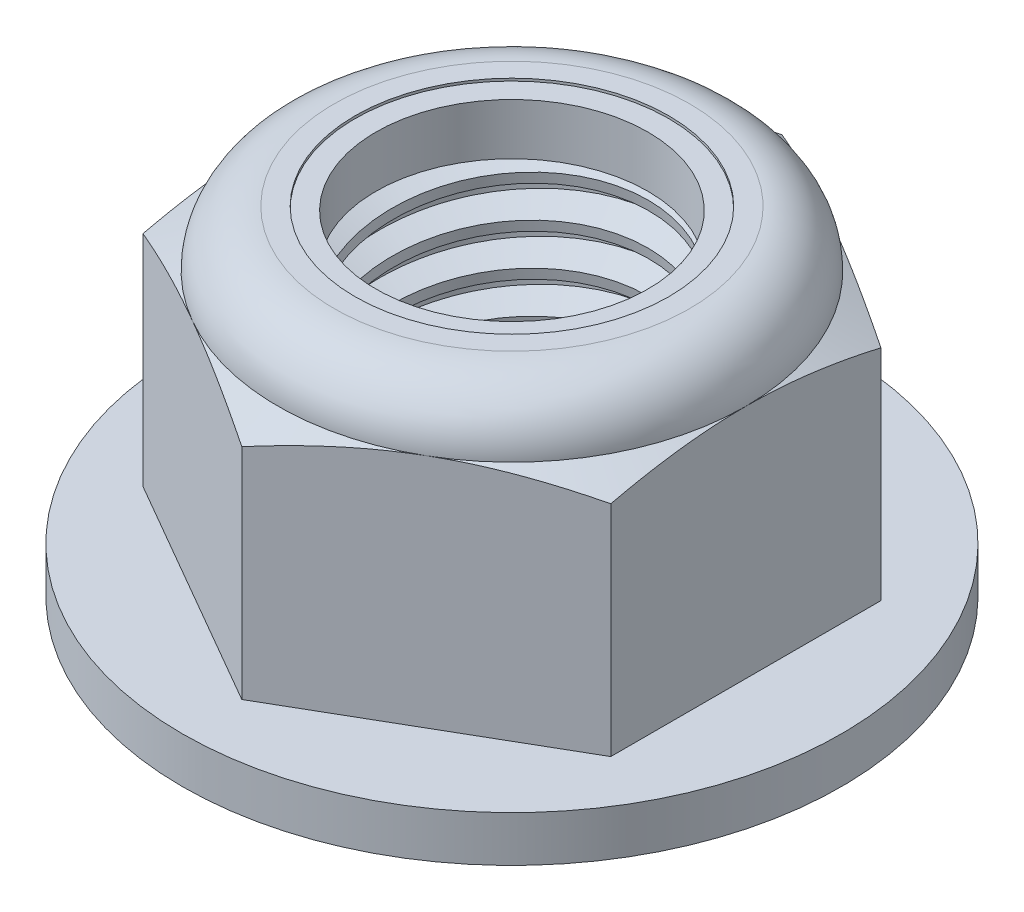
SolidWorks part; units mm, degrees
ref_plane "Front" through (0, 0, 0) normal (0, 0, 1) x (1, 0, 0)
ref_plane "Top" through (0, 0, 0) normal (0, 1, 0) x (1, 0, 0)
ref_plane "Right" through (0, 0, 0) normal (1, 0, 0) x (0, 0, -1)
sketch "Sketch1" plane through (0, 0, 0) normal (0, 1, 0) x (1, 0, 0)
  line L1 (0, 16.4978) -> (-14.2875, 8.2489)
  line L2 (-14.2875, 8.2489) -> (-14.2875, -8.2489)
  line L3 (-14.2875, -8.2489) -> (0, -16.4978)
  line L4 (0, -16.4978) -> (14.2875, -8.2489)
  line L5 (14.2875, -8.2489) -> (14.2875, 8.2489)
  line L6 (14.2875, 8.2489) -> (0, 16.4978)
  circle A0 centre (0, 0) radius 14.2875 construction
  dimension "Hex Flats" = 28.575
extrude "Extrude1" add sketch "Sketch1" along normal blind 20.6375
sketch "Sketch8" plane through (0, 0, 0) normal (1, 0, 0) x (0, 0, -1)
  line L0 (0, 0) -> (20.1295, 0)
  line L1 (20.1295, 0) -> (20.1295, 2.794)
  line L2 (20.1295, 2.794) -> (0, 2.794)
  line L3 (0, 2.794) -> (0, 0)
  line L4 (0, 0) -> (0, -2.794) construction
  dimension "Flange Height" = 2.794
  dimension "Flange Dia" = 40.259
revolve "Revolve3" add sketch "Sketch8" angle 360 about L4
sketch "Sketch2" plane through (0, 0, 0) normal (1, 0, 0) x (0, 0, -1)
  line L0 (-9.525, 0) -> (-9.525, 20.6375) construction
  line L1 (0, 0) -> (9.525, 0)
  line L2 (0, 0) -> (0, 20.6375)
  line L3 (0, 20.6375) -> (9.525, 20.6375)
  line L4 (9.525, 0) -> (9.525, 20.6375)
  line L5 (-8.2489, 20.6375) -> (8.2489, 20.6375) construction
  line L7 (0, -9.525) -> (0, 0) construction
  dimension "Thread Dia" = 19.05
revolve "Revolve1" add sketch "Sketch2" angle 360 about L7
sketch "Sketch3" plane through (0, 0, 0) normal (1, 0, 0) x (0, 0, -1)
  line L0 (9.525, 20.6375) -> (-9.525, 20.6375) construction
  line L1 (-9.525, 20.6375) -> (-9.525, 18.0975) construction
  line L2 (-9.525, 18.0975) -> (9.525, 20.6375) construction
  line L3 (9.525, 20.6375) -> (9.567, 20.3228) construction
  line L4 (9.567, 20.3228) -> (9.8607, 18.1198)
  line L5 (9.8607, 18.1198) -> (8.393, 18.7249)
  line L6 (8.393, 18.7249) -> (8.3091, 19.3543)
  line L7 (8.3091, 19.3543) -> (9.567, 20.3228)
  line L8 (8.3511, 19.0396) -> (9.7138, 19.2213) construction
  line L9 (9.525, 20.6375) -> (9.525, 19.1961) construction
  line L10 (9.525, 19.1961) -> (-9.525, 16.6561) construction
  line L11 (-9.525, 16.6561) -> (-9.525, 18.0975) construction
  line L12 (-0.3615, 20.6375) -> (0.3615, 15.2147) construction
  line L13 (-9.525, 0) -> (-9.525, 20.6375) construction
  line L14 (0, 20.6375) -> (9.525, 20.6375) construction
  line L15 (9.525, 0) -> (9.525, 20.6375) construction
  point P13 (0, 17.9261)
  dimension "D1" = 0.3175
  dimension "D2" = 0.635
  dimension "Thread Pitch" = 2.54
  dimension "D4" = 60
  dimension "D5" = 2.54
revolve "Cut-Revolve1" cut sketch "Sketch3" angle 360 about L12
pattern_linear "LPattern1" count 8 spacing 2.54 along (0, -1, 0) count 2 spacing 2.54 along (0, 1, 0) of "Cut-Revolve1"
sketch "Sketch4" plane through (0, 0, 0) normal (1, 0, 0) x (0, 0, -1)
  line L0 (0, 20.6375) -> (9.525, 20.6375)
  line L1 (9.525, 20.6375) -> (8.3091, 20.0705)
  line L2 (8.3091, 20.0705) -> (8.3091, 0.567)
  line L3 (8.3091, 0.567) -> (9.525, 0)
  line L4 (9.525, 0) -> (0, 0)
  line L5 (0, 0) -> (0, 20.6375)
  line L6 (9.525, 0) -> (9.525, 20.6375) construction
  line L7 (0, 20.6375) -> (9.525, 20.6375) construction
  line L8 (0, 0) -> (9.525, 0) construction
  line L9 (0, 0) -> (0, 20.6375) construction
  line L10 (0, 20.6375) -> (0, 21.9791) construction
  dimension "D1" = 25
revolve "Cut-Revolve2" cut sketch "Sketch4" angle 360 about L10
combine bodies "Combine1" operation type subtract main body 112 bodies to subtract 111
sketch "Sketch5" plane through (0, 0, 0) normal (1, 0, 0) x (0, 0, -1)
  line L0 (20.1295, 2.794) -> (0, 2.794) construction
  line L1 (0, 0) -> (20.1295, 0) construction
  line L2 (16.4978, 2.794) -> (16.4978, 16.1672)
  line L3 (16.4978, 16.1672) -> (14.2875, 17.1979)
  line L4 (10.8479, 20.6375) -> (10.8479, 21.9075)
  line L5 (10.8479, 21.9075) -> (17.7678, 21.9075)
  line L6 (17.7678, 21.9075) -> (17.7678, 2.794)
  line L9 (14.2875, 17.1979) -> (14.2875, 0) construction
  line L13 (16.4978, 2.794) -> (17.7678, 2.794)
  line L15 (0, 0) -> (0, 21.9075) construction
  line L20 (0, 21.9075) -> (10.8479, 21.9075) construction
  line L22 (0, 20.6375) -> (9.525, 20.6375) construction
  arc A0 (14.2875, 17.1979) -> (10.8479, 20.6375) centre (10.8479, 17.1979) ccw
  dimension "D1" = 1.27
  dimension "D2" = 115
  dimension "D3" = 20.6375
  dimension "D4" = 3.4396
revolve "Cut-Revolve3" cut sketch "Sketch5" angle 360 about L15
sketch "Sketch6" plane through (0, 0, 0) normal (1, 0, 0) x (0, 0, -1)
  line L0 (0, 17.1979) -> (14.1351, 17.1979)
  line L1 (10.8479, 20.4851) -> (9.5785, 20.4851)
  line L2 (0, 21.9075) -> (0, 17.1979)
  line L3 (9.5785, 21.9075) -> (0, 21.9075)
  line L4 (0, 21.9075) -> (10.8479, 21.9075) construction
  line L5 (0, 0) -> (0, 21.9075) construction
  line L6 (0, 21.9075) -> (0, 44.323) construction
  line L7 (9.5785, 20.4851) -> (9.5785, 21.9075)
  line L8 (10.8479, 20.6375) -> (10.8479, 20.4851) construction
  line L9 (9.5785, 20.4851) -> (8.3091, 20.4851) construction
  line L10 (8.3091, 20.4851) -> (8.3091, 20.0705) construction
  arc A0 (14.1351, 17.1979) -> (10.8479, 20.4851) centre (10.8479, 17.1979) ccw
  arc A1 (14.2875, 17.1979) -> (10.8479, 20.6375) centre (10.8479, 17.1979) ccw construction
  dimension "D1" = 0.1524
revolve "Cut-Revolve4" cut sketch "Sketch6" angle 360 about L6
sketch "Sketch7" plane through (0, 0, 0) normal (1, 0, 0) x (0, 0, -1)
  line L0 (8.3091, 17.2741) -> (14.058, 17.2741)
  line L1 (10.8479, 20.4089) -> (8.3091, 20.4089)
  line L2 (8.3091, 20.4089) -> (8.3091, 17.2741)
  line L3 (8.3091, 17.2741) -> (0, 17.2741) construction
  line L4 (0, 17.2741) -> (0, 20.4089) construction
  line L5 (0, 20.4089) -> (8.3091, 20.4089) construction
  line L6 (8.3091, 17.2741) -> (8.3091, 17.1979) construction
  line L7 (0, 17.1979) -> (14.1351, 17.1979) construction
  line L8 (10.8479, 20.4089) -> (10.8479, 20.4851) construction
  arc A0 (14.058, 17.2741) -> (10.8479, 20.4089) centre (10.8479, 17.1979) ccw
  arc A2 (14.1351, 17.1979) -> (10.8479, 20.4851) centre (10.8479, 17.1979) ccw construction
  dimension "D1" = 0.0762
revolve "Revolve2" add sketch "Sketch7" angle 360 about L4
equation "\"D1@Sketch3\"=\"Thread Pitch@Sketch3\"/8"
equation "\"D2@Sketch3\"=\"Thread Pitch@Sketch3\"/4"
equation "\"D5@Sketch3\"=\"Thread Pitch@Sketch3\""
equation "\"D4@LPattern1\"=\"Thread Pitch@Sketch3\""
equation "\"D3@LPattern1\"=\"Thread Pitch@Sketch3\""
equation "\"D1@LPattern1\"=\"Height@Extrude1\"/\"Thread Pitch@Sketch3\""
equation "\"D4@Sketch5\"=\"Height@Extrude1\"/6"
